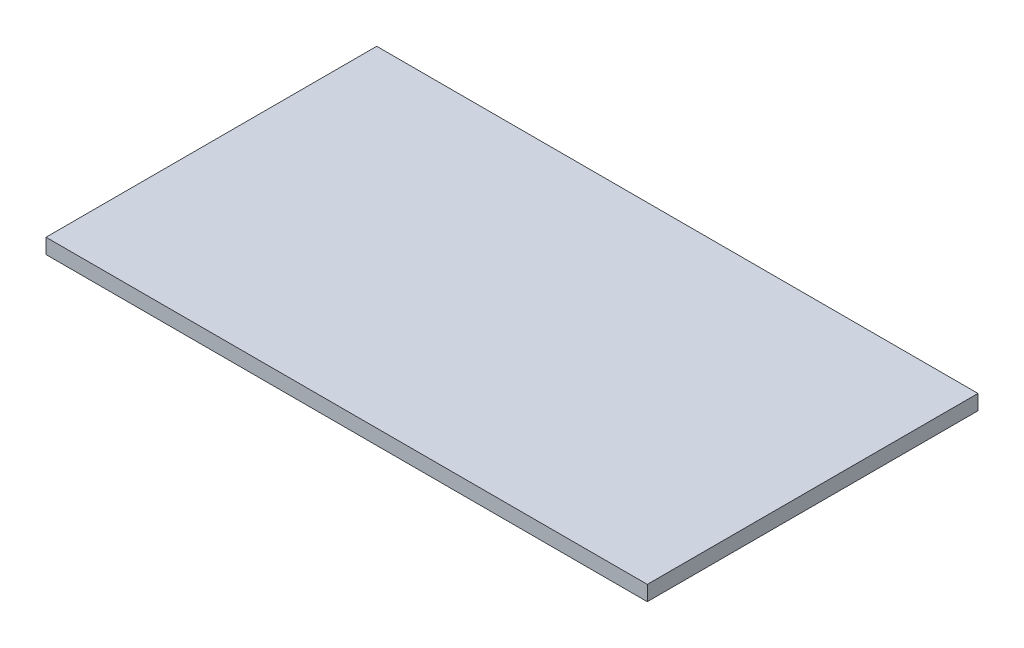
SolidWorks part; units mm, degrees
material "Teck"
ref_plane "Plan de face" through (0, 0, 0) normal (0, 0, 1) x (1, 0, 0)
ref_plane "Plan de dessus" through (0, 0, 0) normal (0, 1, 0) x (1, 0, 0)
ref_plane "Plan de droite" through (0, 0, 0) normal (1, 0, 0) x (0, 0, -1)
sketch "Esquisse1" plane through (0, 0, 0) normal (1, 0, 0) x (0, 0, -1)
  line L1 (-220, 10) -> (220, 10)
  line L2 (-220, 10) -> (-220, -10)
  line L3 (-220, -10) -> (220, -10)
  line L4 (220, 10) -> (220, -10)
  line L5 (-220, 10) -> (220, -10) construction
  line L6 (-220, -10) -> (220, 10) construction
  point P0 (0, 0)
  dimension "D1" = 440
  dimension "D2" = 20
extrude "Boss.-Extru.1" add sketch "Esquisse1" along normal blind 800
